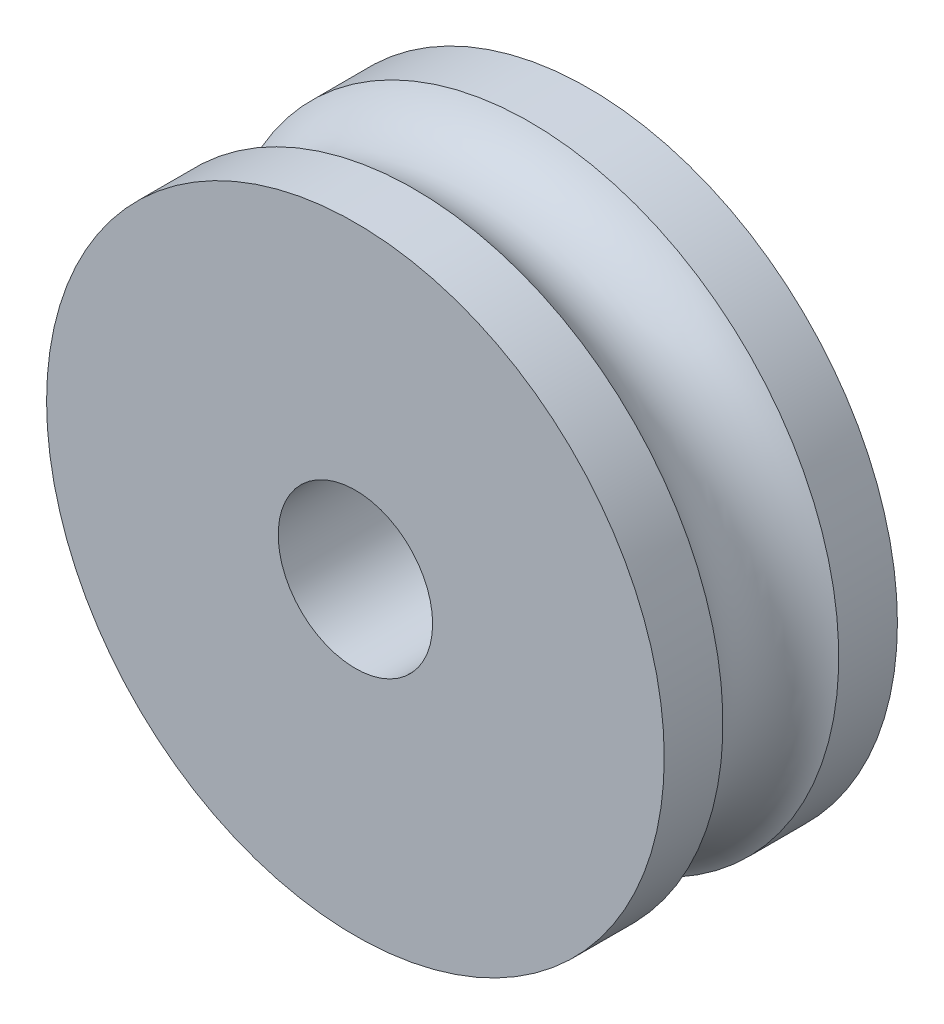
SolidWorks part; units mm, degrees
material "1060 Alloy"
ref_plane "Front Plane" through (0, 0, 0) normal (0, 0, 1) x (1, 0, 0)
ref_plane "Top Plane" through (0, 0, 0) normal (0, 1, 0) x (1, 0, 0)
ref_plane "Right Plane" through (0, 0, 0) normal (1, 0, 0) x (0, 0, -1)
sketch "Sketch1" plane through (0, 0, 0) normal (0, 0, 1) x (1, 0, 0)
  circle A0 centre (0, 0) radius 3.175
  circle A1 centre (0, 0) radius 12.7
  dimension "D1" = 6.35
  dimension "D2" = 25.4
extrude "Boss-Extrude1" add sketch "Sketch1" along normal blind 9.5885
sketch "Sketch2" plane through (0, 0, 0) normal (1, 0, 0) x (0, 0, -1)
  line L0 (0, 12.7) -> (-9.5885, 12.7) construction
  line L1 (-2.413, 12.7) -> (-7.1755, 12.7)
  line L2 (0, 12.7) -> (-9.5885, 12.7) construction
  arc A0 (-2.413, 12.7) -> (-7.1755, 12.7) centre (-4.7942, 14.0087) cw
  point P3 (-4.7942, 12.7)
  point P6 (-4.7943, 11.2915)
  dimension "D1" = 1.4085
  dimension "D2" = 4.7625
ref_axis "Axis1" [suppressed] through (0, 0, -0.6318) along (0, 0, 1)
revolve "Cut-Revolve1" cut sketch "Sketch2" angle 360 about axis through (0, 0, -0.6318) along (0, 0, 1)
